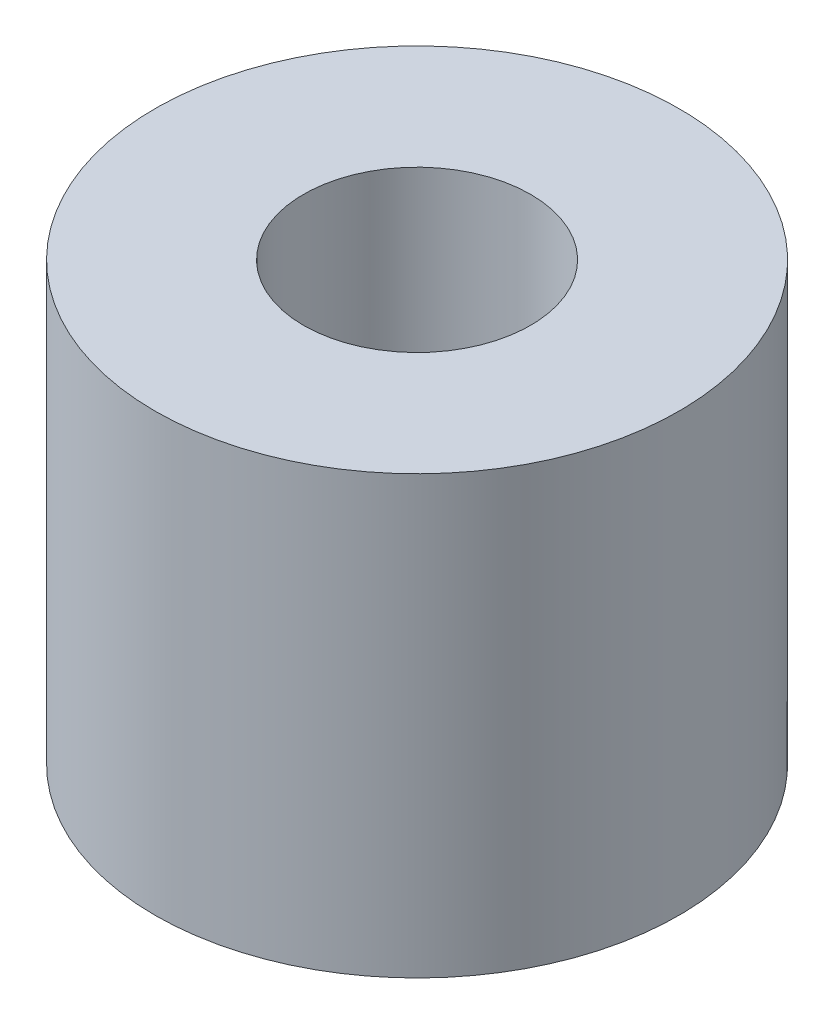
SolidWorks part; units mm, degrees
ref_plane "Front Plane" through (0, 0, 0) normal (0, 0, 1) x (1, 0, 0)
ref_plane "Top Plane" through (0, 0, 0) normal (0, 1, 0) x (1, 0, 0)
ref_plane "Right Plane" through (0, 0, 0) normal (1, 0, 0) x (0, 0, -1)
sketch "Sketch1" plane through (0, 0, 0) normal (0, 1, 0) x (1, 0, 0)
  circle A0 centre (0, 0) radius 1.3
  circle A1 centre (0, 0) radius 3
  dimension "D1" = 2.6
  dimension "D2" = 6
extrude "Boss-Extrude1" add sketch "Sketch1" along normal blind 5
